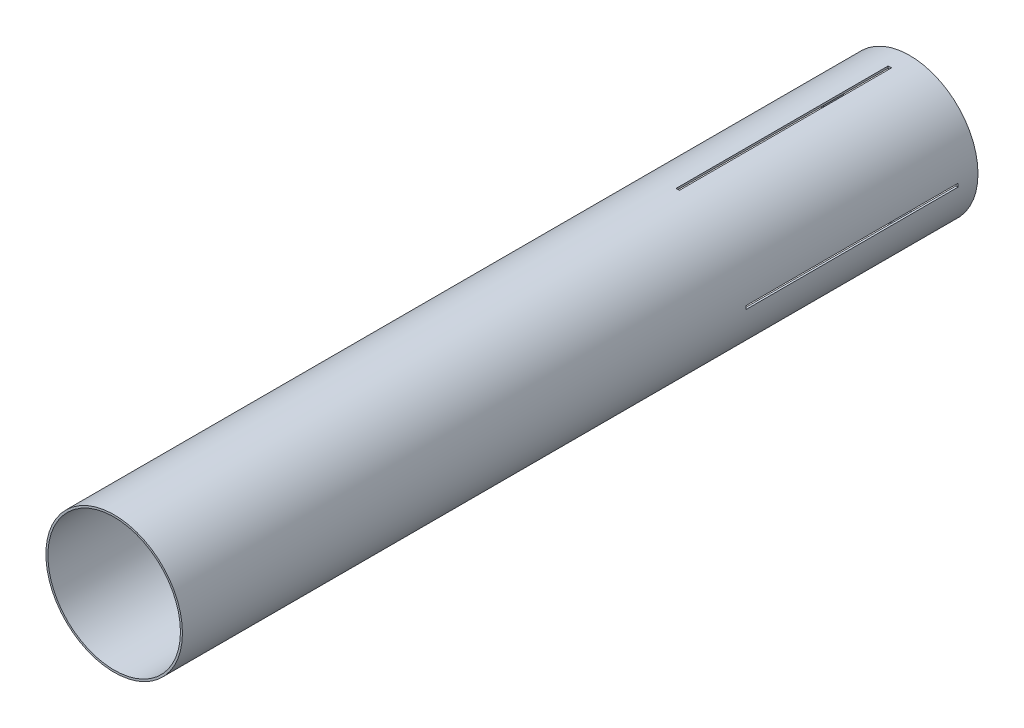
SolidWorks part; units mm, degrees
ref_plane "Front Plane" through (0, 0, 0) normal (0, 0, 1) x (1, 0, 0)
ref_plane "Top Plane" through (0, 0, 0) normal (0, 1, 0) x (1, 0, 0)
ref_plane "Right Plane" through (0, 0, 0) normal (1, 0, 0) x (0, 0, -1)
sketch "Sketch1" plane through (0, 0, 0) normal (0, 0, 1) x (1, 0, 0)
  circle A0 centre (0, 0) radius 65.405
  circle A1 centre (0, 0) radius 63.5
  dimension "D1" = 127
  dimension "D2" = 130.81
extrude "Boss-Extrude1" add sketch "Sketch1" along normal mid plane 762
sketch "Sketch3" plane through (0, 0, 0) normal (0, 1, 0) x (1, 0, 0)
  line L0 (65.405, 381) -> (-65.405, 381) construction
  line L1 (1.5875, 158.75) -> (-1.5875, 158.75)
  line L2 (1.5875, 158.75) -> (1.5875, 361.95)
  line L3 (1.5875, 361.95) -> (-1.5875, 361.95)
  line L4 (-1.5875, 158.75) -> (-1.5875, 361.95)
  line L5 (1.5875, 158.75) -> (-1.5875, 361.95) construction
  line L6 (1.5875, 361.95) -> (-1.5875, 158.75) construction
  line L7 (65.405, 381) -> (-65.405, 381) construction
  point P0 (0, 260.35)
  dimension "D2" = 203.2
  dimension "D3" = 19.05
extrude "Cut-Extrude1" cut sketch "Sketch3" along normal through all
pattern_circular "CirPattern1" count 4 over 360 about axis through (0, 0, 0) along (0, 0, 1) of "Cut-Extrude1"
equation "\"AIRFRAME_OD\"= 5.15in"
equation "\"AIRFRAME_ID\"= 5.00in"
equation "\"FLAT_T\"= 0.125in"
equation "\"NOSE_EXP_L\"= 27in"
equation "\"NOSE_SHOULDER_L\"= 5in"
equation "\"MAIN_L\"= 30in"
equation "\"RECO_COUP_L\"= 10in"
equation "\"RECO_SWITCH_L\"= 2in"
equation "\"DROGUE_L\"= 20in"
equation "\"ATS_FORE_COUP_L\"= 5.5in"
equation "\"ATS_AFT_COUP_L\"= 4.5in"
equation "\"LOWER_L\"= 30in"
equation "\"FIN_N\"= 4"
equation "\"CR_AFT_X\"= 0.5in"
equation "\"CR_FORE_X\"= 9.25in"
equation "\"D1@Sketch1\"=\"AIRFRAME_ID\""
equation "\"D2@Sketch1\"=\"AIRFRAME_OD\""
equation "\"D1@Boss-Extrude1\"=\"LOWER_L\""
equation "\"FIN_ROOT\"= 8in"
equation "\"FIN_X\"= 0.75in"
equation "\"MOTOR_OD\"= 3.091in"
equation "\"MOTOR_ID\"= 3.00in"
equation "\"D1@Sketch3\"=\"FLAT_T\""
equation "\"D2@Sketch3\"=\"FIN_ROOT\""
equation "\"D3@Sketch3\"=\"FIN_X\""
equation "\"D1@CirPattern1\"=\"FIN_N\""
equation "\"COUPLER_OD\"= 4.998in"
equation "\"COUPLER_ID\"= 4.88in"
equation "\"RECO_ROD_X\"= 3.5in"
equation "\"ATS_ROD_X\"= 3.75in"
equation "\"MOTOR_L\"= 14in"
equation "\"MOTOR_LOWER_X\"= 2in"
